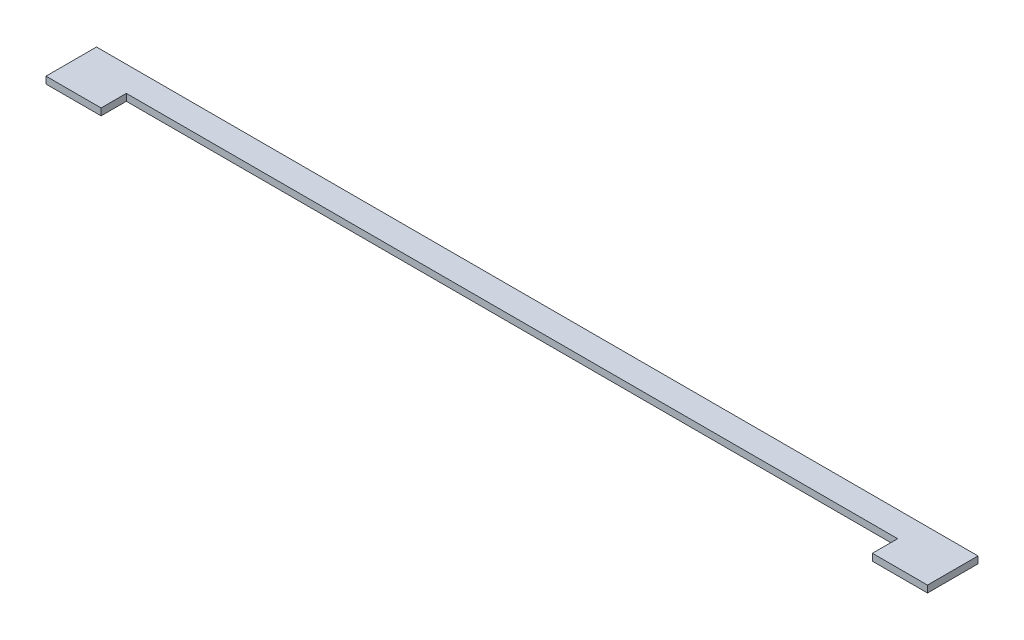
SolidWorks part; units mm, degrees
ref_plane "Front Plane" through (0, 0, 0) normal (0, 0, 1) x (1, 0, 0)
ref_plane "Top Plane" through (0, 0, 0) normal (0, 1, 0) x (1, 0, 0)
ref_plane "Right Plane" through (0, 0, 0) normal (1, 0, 0) x (0, 0, -1)
sketch "Sketch1" plane through (0, 0, 0) normal (0, 1, 0) x (1, 0, 0)
  line L1 (-4487.814, 268.1264) -> (388.986, 268.1264)
  line L2 (-4487.814, 268.1264) -> (-4487.814, 128.4264)
  line L3 (-4487.814, 128.4264) -> (388.986, 128.4264)
  line L4 (388.986, 268.1264) -> (388.986, 128.4264)
  line L5 (-4487.814, 128.4264) -> (-4183.014, 128.4264)
  line L6 (-4487.814, 128.4264) -> (-4487.814, -11.2736)
  line L7 (-4487.814, -11.2736) -> (-4183.014, -11.2736)
  line L8 (-4183.014, 128.4264) -> (-4183.014, -11.2736)
  line L9 (388.986, 128.4264) -> (84.186, 128.4264)
  line L10 (388.986, 128.4264) -> (388.986, -11.2736)
  line L11 (388.986, -11.2736) -> (84.186, -11.2736)
  line L12 (84.186, 128.4264) -> (84.186, -11.2736)
  dimension "D1" = 139.7
  dimension "D2" = 4876.8
  dimension "D3" = 139.7
  dimension "D4" = 304.8
  dimension "D5" = 304.8
  dimension "D6" = 139.7
extrude "Boss-Extrude1" add sketch "Sketch1" along normal blind 38.1 contours L8 L3 L6 L7 | L4 L1 L2 L3 | L3 L12 L11 L10
